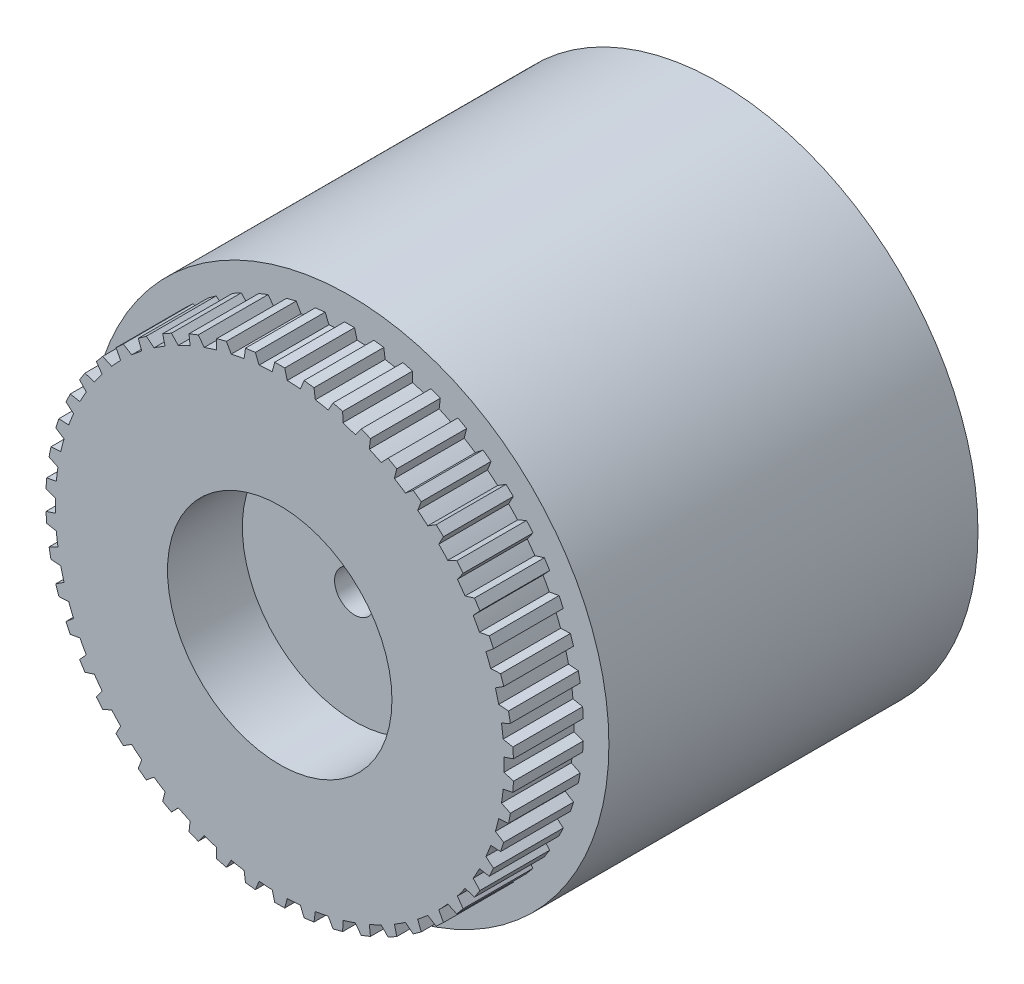
SolidWorks part; units mm, degrees
material "ABS"
ref_plane "Front Plane" through (0, 0, 0) normal (0, 0, 1) x (1, 0, 0)
ref_plane "Top Plane" through (0, 0, 0) normal (0, 1, 0) x (1, 0, 0)
ref_plane "Right Plane" through (0, 0, 0) normal (1, 0, 0) x (0, 0, -1)
sketch "Sketch1" plane through (0, 0, 0) normal (0, 0, 1) x (1, 0, 0)
  circle A0 centre (0, 0) radius 26
  dimension "D1" = 52
extrude "Boss-Extrude1" add sketch "Sketch1" along normal blind 37
sketch "Sketch2" plane through (0, 0, 37) normal (0, 0, 1) x (1, 0, 0)
  circle A0 centre (0, 0) radius 22.5
  dimension "D1" = 45
extrude "Boss-Extrude2" add sketch "Sketch2" along normal blind 7
sketch "Sketch3" plane through (0, 0, 44) normal (0, 0, 1) x (1, 0, 0)
  line L0 (0, 0) -> (0, 23.4454) construction
  line L1 (0, 23.4454) -> (-0.5, 23.4454)
  line L2 (-0.5, 23.4454) -> (-1.7978, 18.6021)
  line L3 (0, 23.4454) -> (0.5, 23.4454)
  line L4 (0.5, 23.4454) -> (1.7978, 18.6021)
  line L5 (1.7978, 18.6021) -> (-1.7978, 18.6021)
  dimension "D1" = 0.5
  dimension "D2" = 0.5
  dimension "D3" = 75
  dimension "D4" = 75
  dimension "D5" = 23.4454
  dimension "D6" = 18.6021
extrude "Boss-Extrude3" add sketch "Sketch3" against normal blind 7
pattern_circular "CirPattern1" count 50 over 360 about axis through (0, 0, 0) along (0, 0, 1) of "Boss-Extrude3"
sketch "Sketch4" plane through (0, 0, 0) normal (0, 0, -1) x (-1, 0, 0)
  circle A0 centre (0, 0) radius 6.75
  dimension "D1" = 13.5
extrude "Cut-Extrude1" cut sketch "Sketch4" against normal blind 5.5
sketch "Sketch5" plane through (0, 0, 5.5) normal (0, 0, -1) x (-1, 0, 0)
  circle A0 centre (0, 0) radius 2
  dimension "D1" = 4
extrude "Cut-Extrude2" cut sketch "Sketch5" against normal through all
sketch "Sketch6" plane through (0, 0, 44) normal (0, 0, 1) x (1, 0, 0)
  circle A0 centre (0, 0) radius 11.25
  dimension "D1" = 22.5
extrude "Cut-Extrude3" cut sketch "Sketch6" against normal blind 7.5
